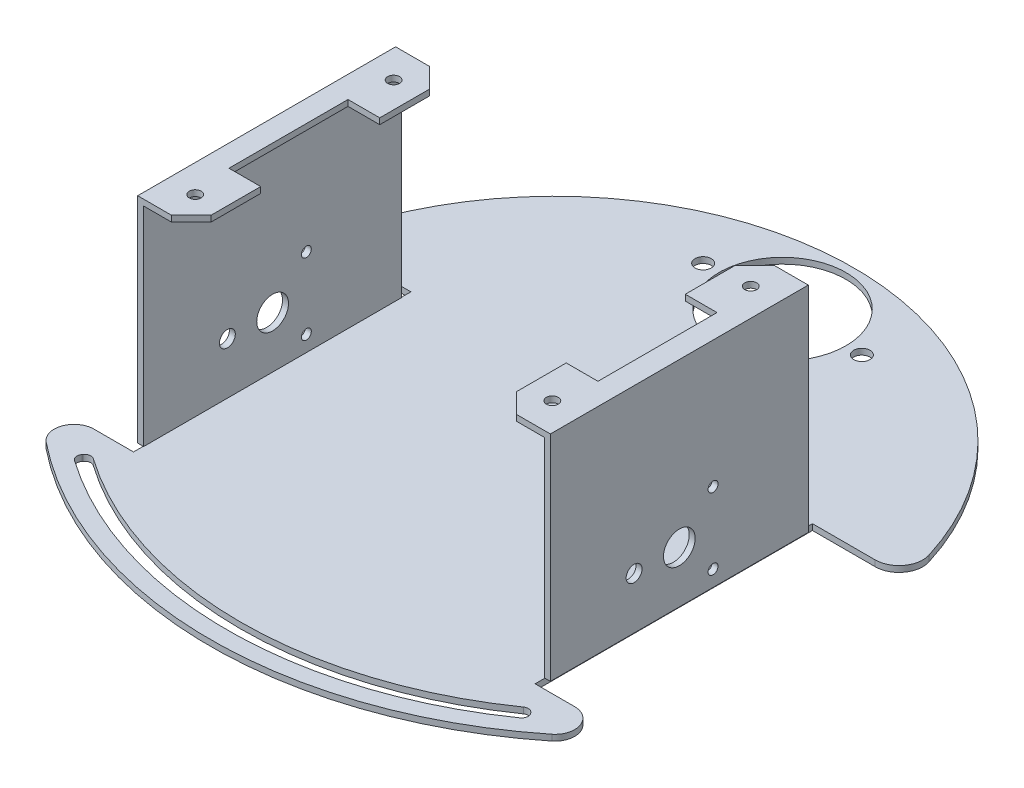
SolidWorks part; units mm, degrees
material "3.3535 (EN-AW 5754)"
ref_plane "Спереди" through (0, 0, 0) normal (0, 0, 1) x (1, 0, 0)
ref_plane "Сверху" through (0, 0, 0) normal (0, 1, 0) x (1, 0, 0)
ref_plane "Справа" through (0, 0, 0) normal (1, 0, 0) x (0, 0, -1)
sketch "Эскиз1" plane through (0, 0, 0) normal (0, 1, 0) x (1, 0, 0)
  line L0 (-50.6, 0) -> (-50.6, 34.95)
  line L1 (-50.6, 0) -> (-50.6, -34.95)
  line L2 (-50.6, -34.95) -> (-56.7978, -34.95)
  line L3 (50.6, 0) -> (50.6, 34.95)
  line L4 (50.6, 0) -> (50.6, -34.95)
  line L5 (50.6, -34.95) -> (60.5883, -34.95)
  line L14 (50.6, 34.95) -> (66.053, 34.95)
  line L15 (50.6, 34.95) -> (66.3145, 34.95)
  line L16 (50.6, 34.95) -> (66.053, 34.95)
  line L17 (50.6, 34.95) -> (66.4232, 34.95)
  line L18 (-50.6, 34.95) -> (-66.4232, 34.95)
  line L19 (-50.6, -34.95) -> (-60.5883, -34.95)
  line L20 (0, 0) -> (0, 1) construction
  line L21 (0, 0) -> (1, 0) construction
  arc A0 (72.1576, 42.7155) -> (-72.1576, 42.7155) centre (0, 20.5) ccw
  circle A1 centre (0, 78) radius 16
  arc A2 (-72.1576, 42.7155) -> (-66.4232, 34.95) centre (-66.4232, 40.95) ccw
  arc A3 (66.4232, 34.95) -> (72.1576, 42.7155) centre (66.4232, 40.95) ccw
  arc A4 (-60.5883, -34.95) -> (-63.7114, -43.8546) centre (-60.5883, -39.95) ccw
  arc A5 (63.7114, -43.8546) -> (60.5883, -34.95) centre (60.5883, -39.95) ccw
  arc A6 (-63.7114, -43.8546) -> (63.7114, -43.8546) centre (0, 35.8) ccw
extrude "Бобышка-Вытянуть1" add sketch "Эскиз1" along normal blind 1.5
sketch "Эскиз3" plane through (0, 0, 0) normal (0, 1, 0) x (1, 0, 0)
  line L0 (-52, 0) -> (-52, 32.5)
  line L1 (-52, 32.5) -> (-50.5, 32.5)
  line L2 (-50.5, 32.5) -> (-50.5, -32.5)
  line L3 (-50.5, -32.5) -> (-52, -32.5)
  line L4 (-52, -32.5) -> (-52, 0)
  line L5 (0, 0) -> (0, -12.5711) construction
  line L6 (0, 0) -> (8.0553, 0) construction
  line L7 (52, -32.5) -> (52, 0)
  line L8 (50.5, -32.5) -> (52, -32.5)
  line L9 (50.5, 32.5) -> (50.5, -32.5)
  line L10 (52, 32.5) -> (50.5, 32.5)
  line L11 (52, 0) -> (52, 32.5)
  dimension "D1" = 1.5
  dimension "D2" = 32.5
  dimension "D3" = 65
  dimension "D4" = 1.5
extrude "Бобышка-Вытянуть2" add sketch "Эскиз3" along normal blind 53.5 from offset 1.5
sketch "Эскиз5" plane through (0, 0, 0) normal (1, 0, 0) x (0, 0, -1)
  line L0 (0, 0) -> (0, 14.5) construction
  circle A0 centre (0, 14.5) radius 4
  dimension "D1" = 14.5
extrude "Вырез-Вытянуть1" cut sketch "Эскиз5" against normal through all and the other way blind 54
sketch "Эскиз6" plane through (0, 0, 0) normal (0, 1, 0) x (1, 0, 0)
  line L0 (0, 0) -> (0, 32.0086) construction
  line L1 (-3.4237, 0) -> (71.1887, 0) construction
  line L3 (-52, 32.5) -> (-52, -32.5) construction
  line L4 (-52, 0) -> (-52, 32.5)
  line L5 (-52, 32.5) -> (-38.5, 32.5)
  line L6 (-38.5, 32.5) -> (-38.5, 0)
  line L7 (-52, 0) -> (-52, -32.5)
  line L8 (-52, -32.5) -> (-38.5, -32.5)
  line L9 (-38.5, -32.5) -> (-38.5, 0)
  line L10 (-38.5, 15) -> (-46.5, 15)
  line L11 (-46.5, 15) -> (-46.5, 0)
  line L12 (-38.5, -15) -> (-46.5, -15)
  line L13 (-46.5, -15) -> (-46.5, 0)
  line L14 (46.5, -15) -> (46.5, 0)
  line L15 (38.5, -15) -> (46.5, -15)
  line L16 (46.5, 15) -> (46.5, 0)
  line L17 (38.5, 15) -> (46.5, 15)
  line L18 (38.5, -32.5) -> (38.5, 0)
  line L19 (52, -32.5) -> (38.5, -32.5)
  line L20 (52, 0) -> (52, -32.5)
  line L21 (38.5, 32.5) -> (38.5, 0)
  line L22 (52, 32.5) -> (38.5, 32.5)
  line L23 (52, 0) -> (52, 32.5)
  dimension "D2" = 30
  dimension "D1" = 13.5
  dimension "D3" = 15
  dimension "D4" = 8
  dimension "D5" = 8
extrude "Бобышка-Вытянуть3" add sketch "Эскиз6" against normal blind 1.5 from offset 55.5 contours L12 L13 L11 L10 L6 L5 L4 L7 L8 L9 | L20 L23 L22 L21 L17 L16 L14 L15 L18 L19
sketch "Эскиз9" plane through (0, 0, 0) normal (0, 1, 0) x (1, 0, 0)
  line L0 (45, 0) -> (-45, 0) construction
  line L1 (-45, -25) -> (-45, 25) construction
  line L2 (0, 0) -> (0, 4.277) construction
  line L3 (45, -25) -> (45, 25) construction
  circle A0 centre (-45, 25) radius 1.5
  circle A1 centre (-45, -25) radius 1.5
  circle A2 centre (45, -25) radius 1.5
  circle A3 centre (45, 25) radius 1.5
  point P12 (0, 0)
  dimension "D1" = 25
  dimension "D2" = 45
extrude "Вырез-Вытянуть2" cut sketch "Эскиз9" along normal through all from offset 50
sketch "Эскиз11" plane through (0, 1.5, 0) normal (0, 1, 0) x (1, 0, 0)
  circle A0 centre (0, 78) radius 20 construction
  circle A1 centre (20, 78) radius 2.05
  circle A2 centre (-20, 78) radius 2.05
  dimension "D1" = 40
  dimension "D2" = 4.1
  dimension "D3" = 4.1
extrude "Вырез-Вытянуть3" cut sketch "Эскиз11" against normal through all
chamfer "Фаска1" distance 5 angle 45 4 edges at (38.5, 54.75, 32.5) (38.5, 54.75, -32.5) (-38.5, 54.75, -32.5) (-38.5, 54.75, 32.5)
sketch "Эскиз12" plane through (0, 0, 0) normal (1, 0, 0) x (0, 0, -1)
  line L2 (0, 14.5) -> (-11.4, 14.5) construction
  line L5 (0, 14.5) -> (8.5, 14.5) construction
  line L6 (8.5, 14.5) -> (8.5, 23.5) construction
  line L7 (8.5, 14.5) -> (8.5, 5.5) construction
  circle A4 centre (-11.4, 14.5) radius 2
  circle A7 centre (8.5, 23.5) radius 1.25
  circle A8 centre (8.5, 5.5) radius 1.25
  dimension "D1" = 2.5
  dimension "D2" = 2.5
  dimension "D3" = 4
  dimension "D4" = 11.4
  dimension "D5" = 8.5
  dimension "D6" = 9
  dimension "D7" = 9
extrude "Вырез-Вытянуть4" cut sketch "Эскиз12" against normal through all both and the other way through all
sketch "Эскиз13" plane through (0, 1.5, 0) normal (0, 1, 0) x (1, 0, 0)
  line L0 (0, 0) -> (0, -12.4995) construction
  line L1 (0, -58.6) -> (0, -62)
  line L2 (0, 35.8) -> (179.8623, -211.7592)
  line L3 (0, 35.8) -> (-179.8623, -211.7592)
  circle A2 centre (0, 35.8) radius 97.8
  circle A3 centre (0, 35.8) radius 94.4
  arc A4 (-63.7114, -43.8546) -> (63.7114, -43.8546) centre (0, 35.8) ccw construction
  circle A6 centre (0, 35.8) radius 96.1 construction
  point P2 (0, -58.6)
  point P4 (0, -62)
  point P7 (0, -66.2)
  point P10 (0, -60.3)
  dimension "D1" = 35.8
  dimension "D2" = 195.6
  dimension "D3" = 188.8
  dimension "D4" = 3.4
  dimension "D5" = 4.2
extrude "Вырез-Вытянуть5" cut sketch "Эскиз13" against normal blind 10 contours A3 L3 A2 L1 | A3 L1 A2 L2
fillet "Скругление1" radius 1.6 4 edges at (-55.4869, 0.75, 40.5712) (-57.4854, 0.75, 43.3219) (57.4854, 0.75, 43.3219) (55.4869, 0.75, 40.5712)
sketch3d "3DSketch1"
  line L0 (0, 0, 0) -> (-10, 0, 0) construction
  line L1 (0, 0, 0) -> (0, 10, 0) construction
  line L2 (0, 0, 0) -> (0, 0, -10) construction
